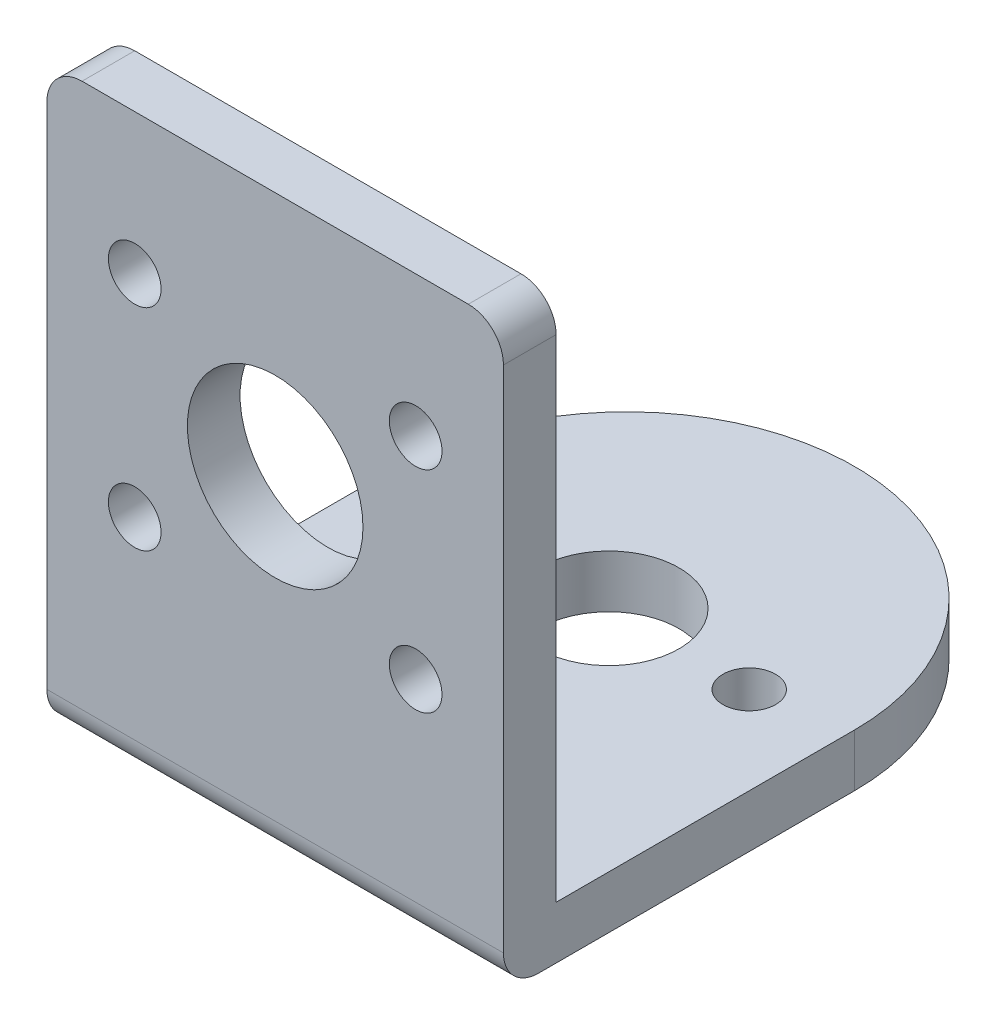
SolidWorks part; units mm, degrees
ref_plane "Front Plane" through (0, 0, 0) normal (0, 0, 1) x (1, 0, 0)
ref_plane "Top Plane" through (0, 0, 0) normal (0, 1, 0) x (1, 0, 0)
ref_plane "Right Plane" through (0, 0, 0) normal (1, 0, 0) x (0, 0, -1)
sketch "Sketch1" plane through (0, 0, 0) normal (0, 0, 1) x (1, 0, 0)
  line L0 (0, 16.5) -> (0, -16.5) construction
  line L1 (-13, -16.5) -> (13, -16.5)
  line L2 (-13, -16.5) -> (-13, 16.5)
  line L3 (-13, 16.5) -> (13, 16.5)
  line L4 (13, -16.5) -> (13, 16.5)
  line L5 (-13, -16.5) -> (13, 16.5) construction
  line L6 (-13, 16.5) -> (13, -16.5) construction
  line L7 (-13, 0) -> (13, 0) construction
  line L8 (-13, 8.5) -> (13, 8.5) construction
  line L9 (-13, -4.7755) -> (13, -4.7755) construction
  line L10 (0, 2.5) -> (13, 2.5) construction
  line L11 (-13, -3.5) -> (13, -3.5) construction
  circle A0 centre (0, 2.5) radius 5
  circle A1 centre (-8, 8.5) radius 1.5
  circle A2 centre (8, 8.5) radius 1.5
  circle A3 centre (8, -3.5) radius 1.5
  circle A4 centre (-8, -3.5) radius 1.5
  point P0 (0, 0)
  dimension "D4" = 10
  dimension "D7" = 3
  dimension "D8" = 3
  dimension "D1" = 26
  dimension "D2" = 33
  dimension "D3" = 14
  dimension "D5" = 8
  dimension "D6" = 16
  dimension "D9" = 6
extrude "Boss-Extrude1" add sketch "Sketch1" along normal blind 3
sketch "Sketch2" plane through (0, 0, 0) normal (0, 0, -1) x (-1, 0, 0)
  line L0 (13, 16.5) -> (13, -16.5) construction
  line L1 (-13, -16.5) -> (13, -16.5)
  line L2 (-13, -16.5) -> (-13, -13.5)
  line L3 (-13, -13.5) -> (13, -13.5)
  line L4 (13, -16.5) -> (13, -13.5)
  dimension "D1" = 3
extrude "Boss-Extrude2" add sketch "Sketch2" along normal blind 30 contours L2 L1 L4 L3
sketch "Sketch3" plane through (0, -13.5, 0) normal (0, 1, 0) x (1, 0, 0)
  line L0 (-13, 16) -> (13, 16) construction
  line L1 (-13, 30) -> (-13, 0) construction
  line L2 (13, 30) -> (13, 0) construction
  line L3 (13, 0) -> (-13, 0) construction
  line L4 (0, 16) -> (0, 30) construction
  line L5 (13, 30) -> (-13, 30) construction
  line L6 (-13, 30) -> (-15.6759, 20.5724)
  line L7 (-13, 30) -> (13, 30)
  line L8 (13, 30) -> (13, 16)
  line L9 (-15.6759, 20.5724) -> (-13, 16)
  circle A0 centre (0, 16) radius 4
  circle A1 centre (-8, 16) radius 1.5
  circle A2 centre (8, 16) radius 1.5
  arc A3 (12.9615, 16) -> (-12.9615, 16) centre (0, 17) ccw
  dimension "D2" = 8
  dimension "D4" = 3
  dimension "D5" = 26
  dimension "D1" = 16
  dimension "D3" = 8
extrude "Cut-Extrude1" cut sketch "Sketch3" against normal through all
fillet "Fillet1" radius 2 2 edges at (13, 16.5, 1.5) (-13, 16.5, 1.5)
fillet "Fillet2" radius 2 1 edges at (0, -16.5, 3)
